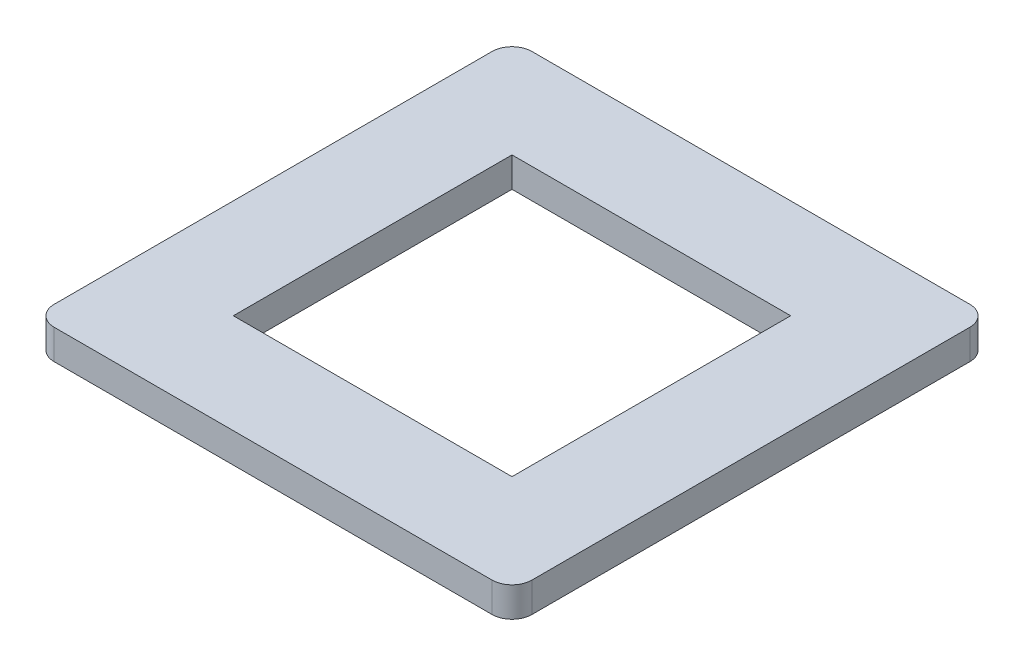
SolidWorks part; units mm, degrees
ref_plane "前视基准面" through (0, 0, 0) normal (0, 0, 1) x (1, 0, 0)
ref_plane "上视基准面" through (0, 0, 0) normal (0, 1, 0) x (1, 0, 0)
ref_plane "右视基准面" through (0, 0, 0) normal (1, 0, 0) x (0, 0, -1)
other "Configuration Table"
sketch "草图1" plane through (0, 0, 0) normal (0, 1, 0) x (1, 0, 0)
  line L0 (-12, -12) -> (-12, 12)
  line L1 (-7, -7) -> (7, -7)
  line L2 (-7, -7) -> (-7, 7)
  line L3 (-7, 7) -> (7, 7)
  line L4 (7, -7) -> (7, 7)
  line L5 (-7, -7) -> (7, 7) construction
  line L6 (-7, 7) -> (7, -7) construction
  line L7 (-12, 12) -> (12, 12)
  line L8 (12, -12) -> (12, 12)
  line L9 (-12, -12) -> (12, -12)
  point P0 (0, 0)
  dimension "D1" = 14
  dimension "D2" = 14
  dimension "D3" = 5
extrude "凸台-拉伸1" add sketch "草图1" along normal blind 1.5
fillet "圆角1" radius 1 4 edges at (12, 0.75, 12) (12, 0.75, -12) (-12, 0.75, -12) (-12, 0.75, 12)
